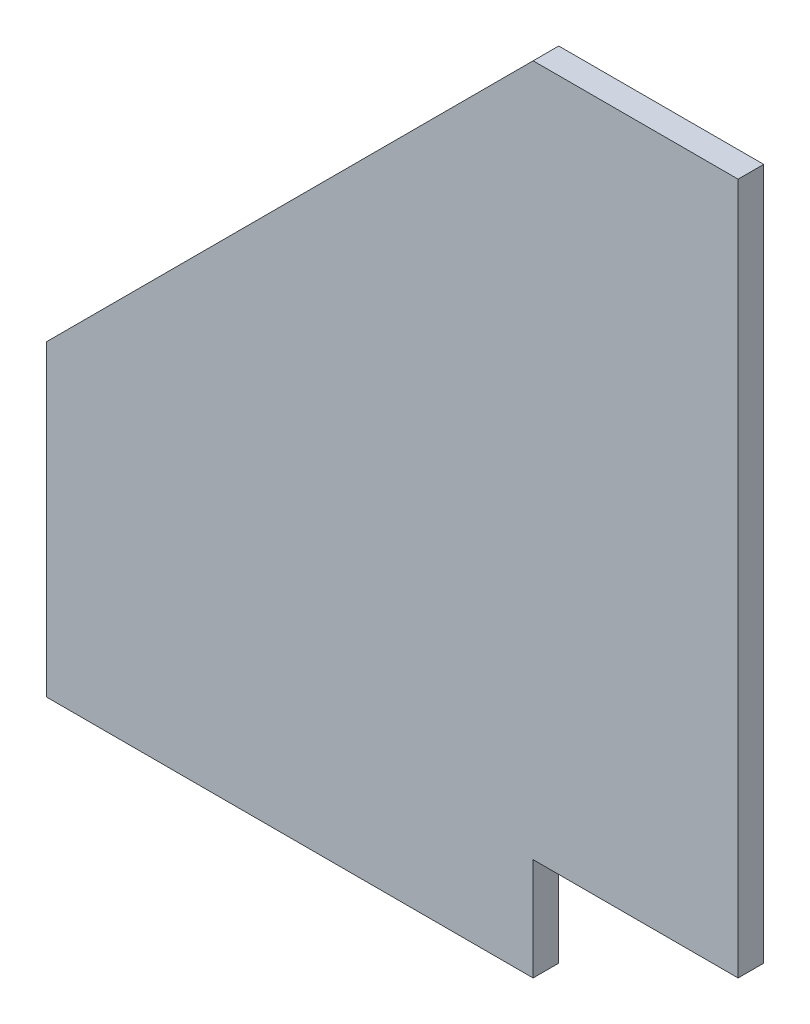
SolidWorks part; units mm, degrees
ref_plane "Front Plane" through (0, 0, 0) normal (0, 0, 1) x (1, 0, 0)
ref_plane "Top Plane" through (0, 0, 0) normal (0, 1, 0) x (1, 0, 0)
ref_plane "Right Plane" through (0, 0, 0) normal (1, 0, 0) x (0, 0, -1)
sketch "Sketch1" plane through (0, 0, 0) normal (0, 0, 1) x (1, 0, 0)
  line L0 (0, 0) -> (120.65, 0)
  line L1 (120.65, 0) -> (120.65, 25.4)
  line L2 (120.65, 25.4) -> (171.45, 25.4)
  line L3 (171.45, 25.4) -> (171.45, 196.85)
  line L5 (171.45, 196.85) -> (120.65, 196.85)
  line L6 (120.65, 196.85) -> (0, 76.2)
  line L7 (0, 76.2) -> (0, 0)
  line L8 (0, 76.2) -> (-76.2, 0) construction
  line L9 (-76.2, 0) -> (0, 0) construction
  dimension "D1" = 25.4
  dimension "D2" = 135
  dimension "D3" = 171.45
  dimension "D4" = 120.65
  dimension "D5" = 50.8
  dimension "D6" = 76.2
  dimension "D7" = 76.2
  dimension "D8" = 120.65
  dimension "D9" = 120.65
extrude "Boss-Extrude1" add sketch "Sketch1" along normal mid plane 6.35
ref_plane "Plane1" through (0, 0, 0) normal (0, 0, -1) x (-1, 0, 0)
ref_plane "Plane2" through (0, 12.7, 0) normal (0, 1, 0) x (1, 0, 0)
